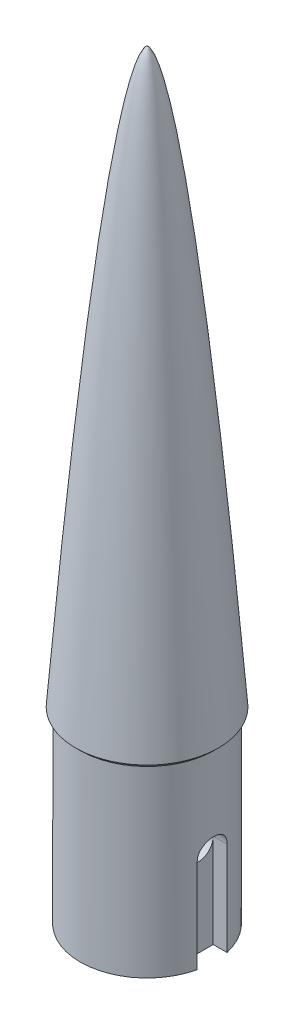
SolidWorks part; units mm, degrees
ref_plane "Front Plane" through (0, 0, 0) normal (0, 0, 1) x (1, 0, 0)
ref_plane "Top Plane" through (0, 0, 0) normal (0, 1, 0) x (1, 0, 0)
ref_plane "Right Plane" through (0, 0, 0) normal (1, 0, 0) x (0, 0, -1)
sketch "Sketch1" plane through (0, 0, 0) normal (0, 1, 0) x (1, 0, 0)
  circle A0 centre (0, 0) radius 8.895
  dimension "D1" = 17.79
extrude "Boss-Extrude1" add sketch "Sketch1" against normal blind 25
sketch "Sketch2" plane through (0, -25, 0) normal (0, -1, 0) x (1, 0, 0)
  line L0 (-6.8312, 1.9844) -> (-6.8312, -1.9844)
  line L1 (-6.8312, 1.9844) -> (-8.6708, 1.9844)
  line L2 (-6.8312, -1.9844) -> (-8.6708, -1.9844)
  line L3 (-8.895, 0) -> (-8.895, -1.1975) construction
  circle A0 centre (0, 0) radius 8.895 construction
  arc A1 (-8.6708, 1.9844) -> (-8.6708, -1.9844) centre (0, 0) ccw
  point P3 (-6.8313, 0)
  dimension "D2" = 3.9688
  dimension "D1" = 2.0637
extrude "Cut-Extrude1" cut sketch "Sketch2" against normal blind 12.5
mirror "Mirror1" about plane through (0, 0, 0) normal (1, 0, 0) of "Cut-Extrude1"
sketch "Sketch3" plane through (0, 0, 0) normal (1, 0, 0) x (0, 0, -1)
  line L0 (1.9844, -12.5) -> (-1.9844, -12.5) construction
  circle A0 centre (0, -12.5) radius 1.9844
extrude "Cut-Extrude2" cut sketch "Sketch3" against normal through all both and the other way through all
sketch "Sketch4" plane through (0, 0, 0) normal (0, 0, 1) x (1, 0, 0)
  line L0 (0, 0) -> (0, 76.2)
  line L1 (9.5, 0) -> (0, 0)
  spline S0 degree 4 poles (0, 76.2) (0.0108, 76.1992) (0.0319, 76.1957) (0.0723, 76.1802) (0.1209, 76.1494) (0.1689, 76.1095) (0.2195, 76.0586) (0.2709, 75.9991) (0.3341, 75.9153) (0.4169, 75.7887) (0.5301, 75.5875) (0.6908, 75.2504) (0.9252, 74.6604) (1.2807, 73.5641) (1.8193, 71.4845) (2.4946, 68.1697) (3.2291, 63.7611) (3.9741, 58.5076) (4.6716, 52.9667) (5.31, 47.384) (5.8981, 41.8504) (6.4564, 36.2256) (6.9744, 30.7409) (7.4852, 25.0194) (7.9461, 19.6817) (8.4361, 13.7069) (8.8315, 8.7821) (9.3022, 2.6463) (9.5557, -0.7315) (9.8071, -4.1458) (9.9709, -6.3901) (10.0134, -6.991) (10.0631, -7.6734) knots 0 0 0 0 0 0.000506 0.001013 0.002025 0.002702 0.00345 0.004398 0.005735 0.007655 0.010586 0.015299 0.023344 0.037633 0.064933 0.116773 0.182859 0.248945 0.315031 0.381117 0.447202 0.513288 0.579374 0.64546 0.711546 0.777632 0.843718 0.909803 0.954902 0.977451 1 1 1 1 1 construction
  spline S1 degree 4 poles (0, 76.2) (0.0108, 76.1992) (0.0319, 76.1957) (0.0723, 76.1802) (0.1209, 76.1494) (0.1689, 76.1095) (0.2195, 76.0586) (0.2709, 75.9991) (0.3341, 75.9153) (0.4169, 75.7887) (0.5301, 75.5875) (0.6908, 75.2504) (0.9252, 74.6604) (1.2807, 73.5641) (1.8193, 71.4845) (2.4946, 68.1697) (3.2291, 63.7611) (3.9741, 58.5076) (4.6716, 52.9667) (5.31, 47.384) (5.8981, 41.8504) (6.4564, 36.2256) (6.9744, 30.7409) (7.4852, 25.0194) (7.9461, 19.6817) (8.4361, 13.7069) (8.8315, 8.7821) (9.215, 3.7834) (9.405, 1.2697) (9.5, 0) knots 0 0 0 0 0 0.000506 0.001013 0.002025 0.002702 0.00345 0.004398 0.005735 0.007655 0.010586 0.015299 0.023344 0.037633 0.064933 0.116773 0.182859 0.248945 0.315031 0.381117 0.447202 0.513288 0.579374 0.64546 0.711546 0.777632 0.843718 0.909803 0.909803 0.909803 0.909803 0.909803
  dimension "D1" = 76.2
  dimension "D2" = 9.5
revolve "Revolve1" add sketch "Sketch4" angle 360 about L0
chamfer "Chamfer1" distance 0.6 angle 45 1 edges at (0, 0, 8.895)
equation "\"D_SHOULDER\"= 17.79mm"
equation "\"OD_AIRF\"= 19mm"
equation "\"W_CORD\"= 3.175mm"
equation "\"L_SHOULDER\"= 25mm"
equation "\"L_CONE\"= 3in"
equation "\"D1@Sketch1\"=\"D_SHOULDER\""
equation "\"D1@Boss-Extrude1\"=\"L_SHOULDER\""
equation "\"D2@Sketch2\"=1.25*\"W_CORD\""
equation "\"D1@Sketch2\"=0.65*\"W_CORD\""
equation "\"D1@Cut-Extrude1\"=\"L_SHOULDER\"/2"
equation "\"D1@Sketch4\"=\"L_CONE\""
